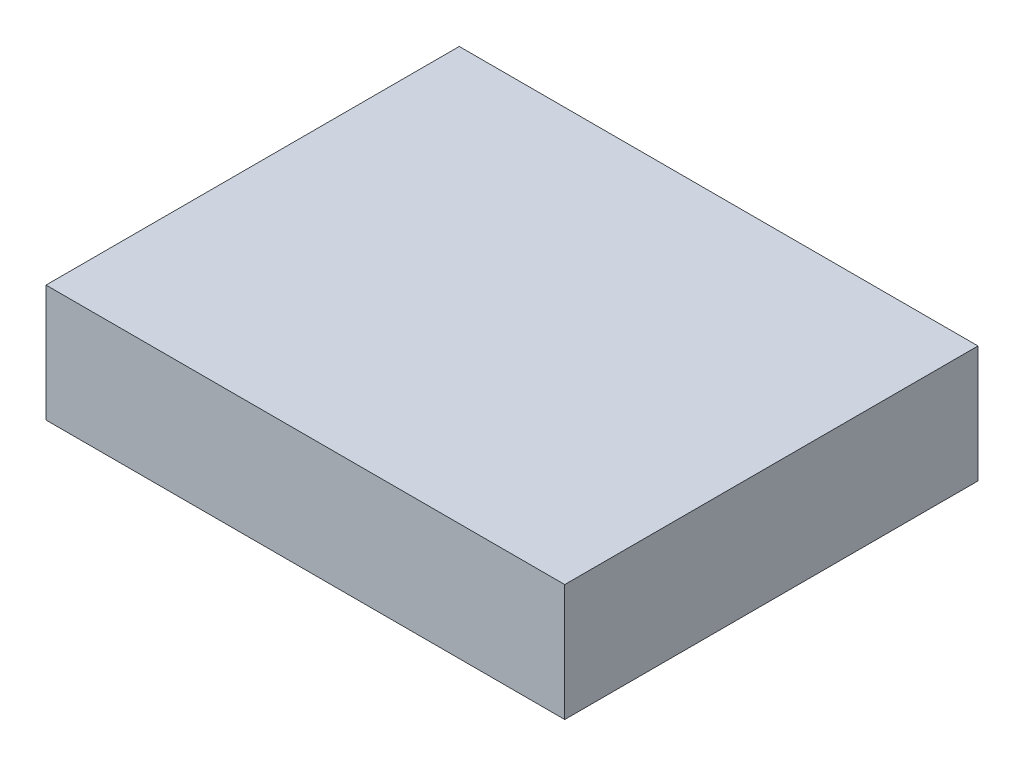
SolidWorks part; units mm, degrees
ref_plane "Front Plane" through (0, 0, 0) normal (0, 0, 1) x (1, 0, 0)
ref_plane "Top Plane" through (0, 0, 0) normal (0, 1, 0) x (1, 0, 0)
ref_plane "Right Plane" through (0, 0, 0) normal (1, 0, 0) x (0, 0, -1)
sketch "Sketch1" plane through (0, 0, 0) normal (0, 1, 0) x (1, 0, 0)
  line L1 (-47.7, -38) -> (47.7, -38)
  line L2 (-47.7, -38) -> (-47.7, 38)
  line L3 (-47.7, 38) -> (47.7, 38)
  line L4 (47.7, -38) -> (47.7, 38)
  line L5 (-47.7, -38) -> (47.7, 38) construction
  line L6 (-47.7, 38) -> (47.7, -38) construction
  point P0 (0, 0)
  dimension "D1" = 76
  dimension "D2" = 95.4
extrude "Boss-Extrude1" add sketch "Sketch1" along normal blind 21.5
